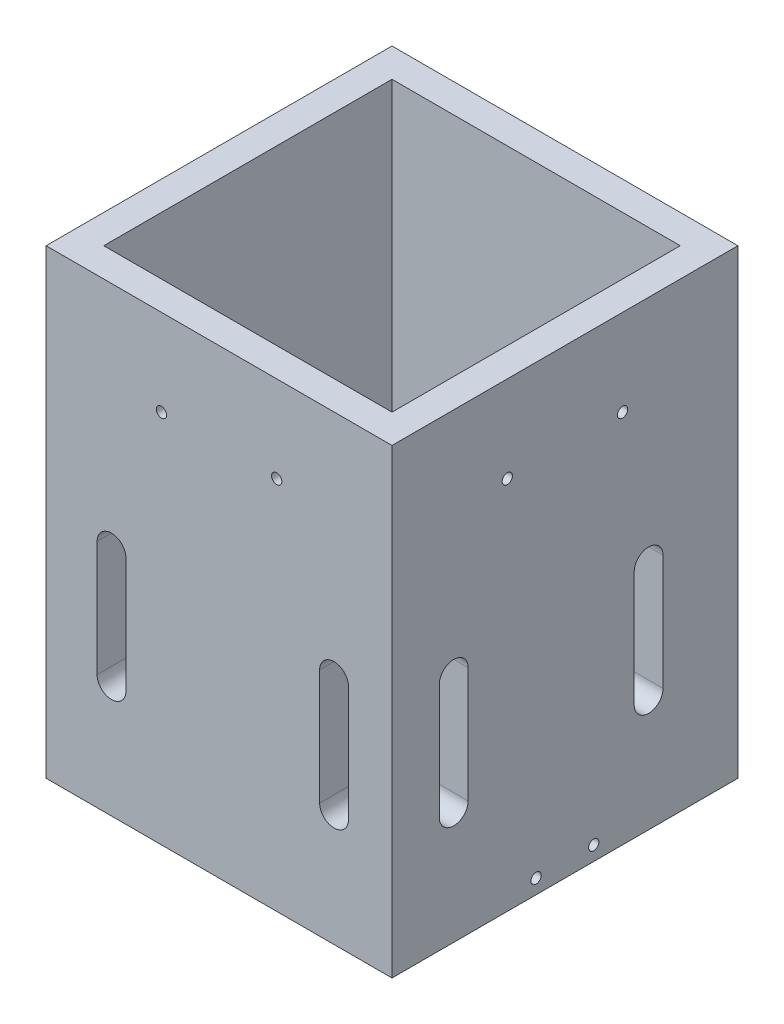
SolidWorks part; units mm, degrees
material "6061 Alloy"
ref_plane "Front Plane" through (0, 0, 0) normal (0, 0, 1) x (1, 0, 0)
ref_plane "Top Plane" through (0, 0, 0) normal (0, 1, 0) x (1, 0, 0)
ref_plane "Right Plane" through (0, 0, 0) normal (1, 0, 0) x (0, 0, -1)
sketch "Sketch2" plane through (0, 0, 0) normal (0, 1, 0) x (1, 0, 0)
  line L1 (-39.4322, 32.949) -> (36.7678, 32.949)
  line L2 (-39.4322, 32.949) -> (-39.4322, -43.251)
  line L3 (-39.4322, -43.251) -> (36.7678, -43.251)
  line L4 (36.7678, 32.949) -> (36.7678, -43.251)
  dimension "D1" = 76.2
  dimension "D2" = 76.2
extrude "Boss-Extrude1" add sketch "Sketch2" along normal blind 101.6
sketch "Sketch3" plane through (0, 101.6, 0) normal (0, 1, 0) x (1, 0, 0)
  line L0 (-39.4322, 32.949) -> (-39.4322, -43.251) construction
  line L1 (-33.0822, 26.599) -> (30.4178, 26.599)
  line L2 (-33.0822, 26.599) -> (-33.0822, -36.901)
  line L3 (-33.0822, -36.901) -> (30.4178, -36.901)
  line L4 (30.4178, 26.599) -> (30.4178, -36.901)
  line L5 (36.7678, 32.949) -> (-39.4322, 32.949) construction
  line L6 (-39.4322, -43.251) -> (36.7678, -43.251) construction
  line L7 (36.7678, -43.251) -> (36.7678, 32.949) construction
  dimension "D1" = 6.35
  dimension "D2" = 6.35
  dimension "D3" = 6.35
  dimension "D4" = 6.35
extrude "Cut-Extrude1" cut sketch "Sketch3" against normal through all
sketch "Sketch4" plane through (0, 0, 43.251) normal (0, 0, 1) x (1, 0, 0)
  line L0 (-25.0177, 25.4) -> (-25.0177, 50.8) construction
  line L1 (-28.1927, 25.4) -> (-28.1927, 50.8)
  line L2 (-21.8427, 25.4) -> (-21.8427, 50.8)
  line L4 (-39.4322, 101.6) -> (-39.4322, 0) construction
  line L5 (24.0043, 25.4) -> (24.0043, 50.8) construction
  line L6 (20.8293, 25.4) -> (20.8293, 50.8)
  line L7 (27.1793, 25.4) -> (27.1793, 50.8)
  line L8 (-39.4322, 0) -> (36.7678, 0) construction
  arc A0 (-28.1927, 25.4) -> (-21.8427, 25.4) centre (-25.0177, 25.4) ccw
  arc A1 (-21.8427, 50.8) -> (-28.1927, 50.8) centre (-25.0177, 50.8) ccw
  arc A2 (20.8293, 25.4) -> (27.1793, 25.4) centre (24.0043, 25.4) ccw
  arc A3 (27.1793, 50.8) -> (20.8293, 50.8) centre (24.0043, 50.8) ccw
  point P2 (-25.0177, 38.1)
  point P14 (24.0043, 38.1)
  dimension "D1" = 25.4
  dimension "D2" = 38.1
  dimension "D3" = 6.35
  dimension "D4" = 14.4145
  dimension "D5" = 2
extrude "Cut-Extrude2" cut sketch "Sketch4" against normal up to next
sketch "Sketch5" plane through (36.7678, 0, 0) normal (1, 0, 0) x (0, 0, -1)
  line L0 (-29.6493, 25.4) -> (-29.6493, 50.8) construction
  line L1 (-32.8243, 25.4) -> (-32.8243, 50.8)
  line L2 (-26.4743, 25.4) -> (-26.4743, 50.8)
  line L4 (-43.251, 101.6) -> (-43.251, 0) construction
  line L5 (13.2767, 25.4) -> (13.2767, 50.8) construction
  line L6 (10.1017, 25.4) -> (10.1017, 50.8)
  line L7 (16.4517, 25.4) -> (16.4517, 50.8)
  line L8 (-43.251, 0) -> (32.949, 0) construction
  arc A0 (-32.8243, 25.4) -> (-26.4743, 25.4) centre (-29.6493, 25.4) ccw
  arc A1 (-26.4743, 50.8) -> (-32.8243, 50.8) centre (-29.6493, 50.8) ccw
  arc A2 (10.1017, 25.4) -> (16.4517, 25.4) centre (13.2767, 25.4) ccw
  arc A3 (16.4517, 50.8) -> (10.1017, 50.8) centre (13.2767, 50.8) ccw
  point P2 (-29.6493, 38.1)
  point P15 (13.2767, 38.1)
  dimension "D1" = 38.1
  dimension "D2" = 13.6017
  dimension "D3" = 6.35
  dimension "D4" = 25.4
  dimension "D5" = 2
extrude "Cut-Extrude3" cut sketch "Sketch5" against normal up to next
hole_wizard "#4-40 Tapped Hole1" positions "Sketch7" profile "Sketch6" tap size "#4-40" standard "ANSI Inch" end condition up to next
sketch "Sketch7" plane through (0, 0, 43.251) normal (0, 0, 1) x (1, 0, 0)
  line L0 (-39.4322, 101.6) -> (36.7678, 101.6) construction
  line L1 (-39.4322, 101.6) -> (-39.4322, 0) construction
  line L2 (36.7678, 101.6) -> (36.7678, 0) construction
  point P0 (-14.0322, 82.55)
  point P2 (11.3678, 82.55)
  dimension "D1" = 19.05
  dimension "D2" = 25.4
  dimension "D3" = 25.4
  dimension "D4" = 19.05
cosmetic thread "Hole Thread1" parameters "D2"=2.8448
cosmetic thread "Hole Thread2" parameters "D2"=2.8448
sketch "Sketch6" plane through (-14.0322, 82.55, 43.251) normal (1, 0, 0) x (0, -1, 0)
  line L0 (0, 0) -> (0, 6.35)
  line L1 (0, 6.35) -> (1.1303, 6.35)
  line L2 (1.1303, 6.35) -> (1.1303, 0)
  line L5 (1.1303, 0) -> (0, 0)
  line L11 (0, -6.35) -> (0, 107.95) construction
  dimension "Thru Tap Drill Dia." = 2.2606
  dimension "Thru Tap Drill Depth" = 6.35
hole_wizard "#4-40 Tapped Hole2" positions "Sketch9" profile "Sketch8" tap size "#4-40" standard "ANSI Inch" end condition up to next
sketch "Sketch9" plane through (36.7678, 0, 0) normal (1, 0, 0) x (0, 0, -1)
  line L0 (-43.251, 101.6) -> (32.949, 101.6) construction
  line L1 (32.949, 101.6) -> (32.949, 0) construction
  line L2 (-43.251, 101.6) -> (-43.251, 0) construction
  point P0 (-17.851, 82.55)
  point P2 (7.549, 82.55)
  dimension "D1" = 19.05
  dimension "D2" = 19.05
  dimension "D3" = 25.4
  dimension "D4" = 25.4
sketch "Sketch8" plane through (36.7678, 82.55, 17.851) normal (0, 1, 0) x (0, 0, -1)
  line L0 (0, 0) -> (0, 6.35)
  line L1 (0, 6.35) -> (1.1303, 6.35)
  line L2 (1.1303, 6.35) -> (1.1303, 0)
  line L5 (1.1303, 0) -> (0, 0)
  line L11 (0, -6.35) -> (0, 107.95) construction
  dimension "Thru Tap Drill Dia." = 2.2606
  dimension "Thru Tap Drill Depth" = 6.35
cosmetic thread "Hole Thread3" parameters "D2"=2.8448
cosmetic thread "Hole Thread4" parameters "D2"=2.8448
hole_wizard "#4-40 Tapped Hole3" positions "Sketch11" profile "Sketch10" tap size "#4-40" standard "ANSI Inch" end condition through all
sketch "Sketch11" plane through (36.7678, 0, 0) normal (1, 0, 0) x (0, 0, -1)
  line L0 (32.949, 101.6) -> (32.949, 0) construction
  line L1 (-43.251, 101.6) -> (-43.251, 0) construction
  line L2 (32.949, 0) -> (-43.251, 0) construction
  point P0 (1.199, 3.175)
  point P2 (-11.501, 3.175)
  dimension "D1" = 31.75
  dimension "D2" = 31.75
  dimension "D3" = 3.175
  dimension "D4" = 3.175
sketch "Sketch10" plane through (36.7678, 3.175, -1.199) normal (0, 1, 0) x (0, 0, -1)
  line L0 (0, 0) -> (0, 76.2)
  line L1 (0, 76.2) -> (1.1303, 76.2)
  line L2 (1.1303, 76.2) -> (1.1303, 0)
  line L5 (1.1303, 0) -> (0, 0)
  line L11 (0, -6.35) -> (0, 107.95) construction
  dimension "Thru Tap Drill Dia." = 2.2606
  dimension "Thru Tap Drill Depth" = 76.2
cosmetic thread "Hole Thread5" parameters "D2"=2.8448
cosmetic thread "Hole Thread6" parameters "D2"=2.8448
